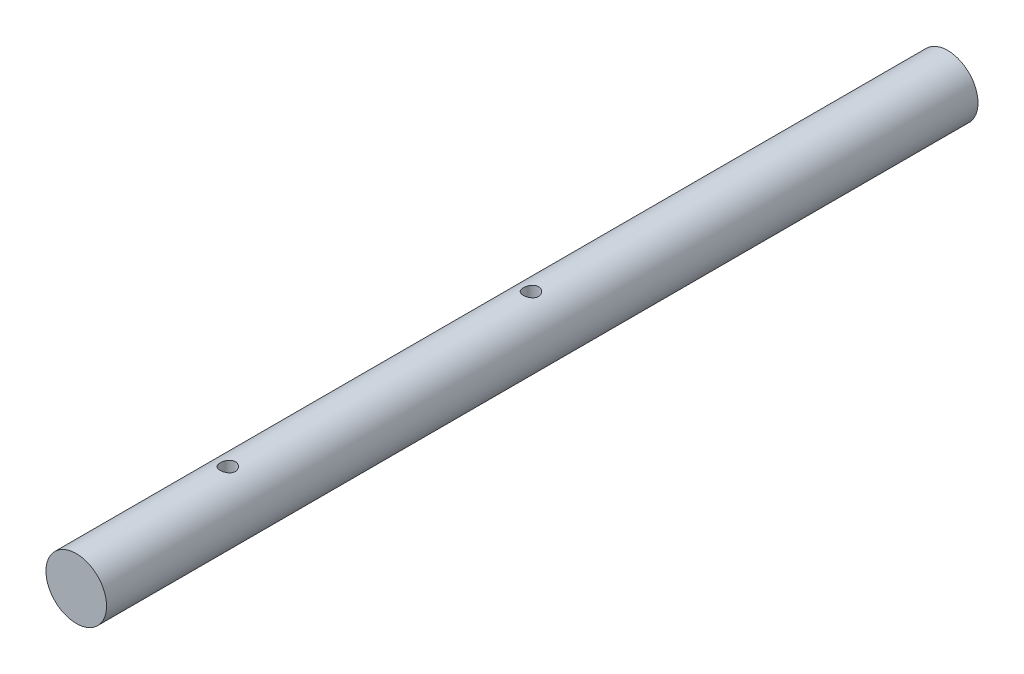
SolidWorks part; units mm, degrees
ref_plane "前视基准面" through (0, 0, 0) normal (0, 0, 1) x (1, 0, 0)
ref_plane "上视基准面" through (0, 0, 0) normal (0, 1, 0) x (1, 0, 0)
ref_plane "右视基准面" through (0, 0, 0) normal (1, 0, 0) x (0, 0, -1)
sketch "草图1" plane through (0, 0, 0) normal (0, 0, 1) x (1, 0, 0)
  circle A0 centre (-17.8141, 40.7356) radius 8
  dimension "D1" = 16
extrude "凸台-拉伸1" add sketch "草图1" along normal blind 230
sketch "草图2" plane through (0, 0, 0) normal (0, 1, 0) x (1, 0, 0)
  line L5 (-17.8141, -110) -> (-17.8141, -190) construction
  circle A1 centre (-17.8141, -110) radius 2
  circle A2 centre (-17.8141, -190) radius 2
  point P12 (0, 0)
  dimension "D4" = 4
  dimension "D6" = 4
  dimension "D5" = 80
extrude "切除-拉伸1" cut sketch "草图2" along normal blind 148
